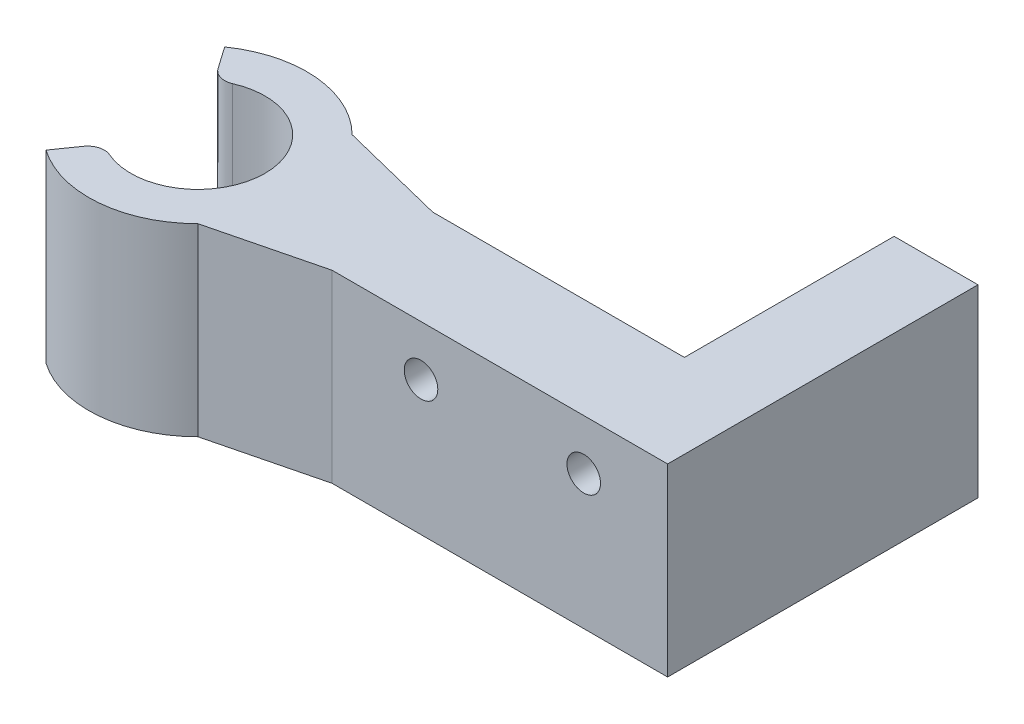
SolidWorks part; units mm, degrees
ref_plane "Plan de face" through (0, 0, 0) normal (0, 0, 1) x (1, 0, 0)
ref_plane "Plan de dessus" through (0, 0, 0) normal (0, 1, 0) x (1, 0, 0)
ref_plane "Plan de droite" through (0, 0, 0) normal (1, 0, 0) x (0, 0, -1)
sketch "Esquisse1" plane through (0, 0, 0) normal (0, 1, 0) x (1, 0, 0)
  line L0 (0, 6.5) -> (0, -6.5) construction
  line L1 (21, 0) -> (0, 0) construction
  line L2 (0, 0) -> (-3.7282, 5.3245) construction
  line L3 (0, 0) -> (-3.7282, -5.3245) construction
  line L4 (11, 3) -> (31, 3)
  line L5 (11, 3) -> (11, -3)
  line L6 (11, -3) -> (31, -3)
  line L7 (31, 3) -> (31, -3)
  line L8 (11, 3) -> (31, -3) construction
  line L9 (11, -3) -> (31, 3) construction
  line L10 (0, 0) -> (4.5962, 4.5962) construction
  line L11 (4.5962, 4.5962) -> (11, 3)
  line L12 (0, 0) -> (4.5962, -4.5962) construction
  line L13 (11, -3) -> (4.5962, -4.5962)
  line L14 (-3.7282, -5.3245) -> (-2.8099, -4.013)
  line L15 (-3.7282, 5.3245) -> (-2.8099, 4.013)
  arc A0 (-1.5926, -3.6693) -> (-1.5926, 3.6693) centre (0, 0) ccw
  arc A1 (-3.7282, -5.3245) -> (4.5962, -4.5962) centre (0, 0) ccw
  arc A2 (4.5962, 4.5962) -> (-3.7282, 5.3245) centre (0, 0) ccw
  arc A3 (-1.5926, -3.6693) -> (-2.8099, -4.013) centre (-1.9908, -4.5866) ccw
  arc A4 (-1.5926, 3.6693) -> (-2.8099, 4.013) centre (-1.9908, 4.5866) cw
  point P1 (21, 0)
  point P4 (0, 6.5)
  point P14 (4, 0)
  point P20 (-2.2943, -3.2766)
  point P23 (-2.2943, 3.2766)
  dimension "D1" = 4
  dimension "D2" = 13
  dimension "D10" = 1
  dimension "D3" = 35
  dimension "D4" = 35
  dimension "D5" = 7
  dimension "D6" = 6
  dimension "D7" = 20
  dimension "D8" = 45
  dimension "D9" = 45
extrude "Boss.-Extru.1" add sketch "Esquisse1" along normal blind 11 contours L11 A2 L15 A0 L14 A1 L13 L5 | L7 L4 L5 L6
sketch "Esquisse2" plane through (0, 0, 3) normal (0, 0, 1) x (1, 0, 0)
  line L0 (16.3, 8) -> (26, 8) construction
  line L1 (11, 11) -> (31, 11) construction
  line L2 (31, 11) -> (31, 0) construction
  circle A0 centre (16.3, 8) radius 1
  circle A1 centre (26, 8) radius 1
  dimension "D2" = 2
  dimension "D1" = 9.7
  dimension "D3" = 3
  dimension "D4" = 5
extrude "Enlèv. mat.-Extru.1" cut sketch "Esquisse2" against normal blind 4
sketch "Esquisse3" plane through (0, 0, -3) normal (0, 0, -1) x (-1, 0, 0)
  line L0 (-31, 11) -> (-31, 0) construction
  line L1 (-26, 11) -> (-31, 11)
  line L2 (-26, 11) -> (-26, 0)
  line L3 (-26, 0) -> (-31, 0)
  line L4 (-31, 11) -> (-31, 0)
  line L5 (-26, 11) -> (-31, 0) construction
  line L6 (-26, 0) -> (-31, 11) construction
  line L7 (7.15, 0) -> (-7.15, 0) construction
  line L8 (-11, 11) -> (-31, 11) construction
  point P0 (-28.5, 5.5)
  dimension "D1" = 5
extrude "Boss.-Extru.2" add sketch "Esquisse3" along normal blind 12.5
equation "\"D4@Esquisse1\"=\"D3@Esquisse1\""
